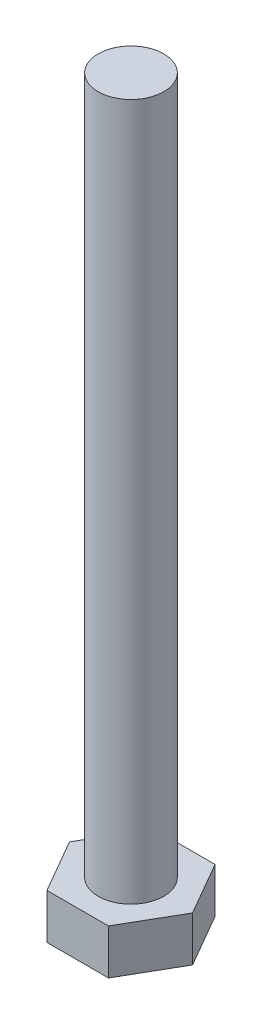
SolidWorks part; units mm, degrees
material "Plain Carbon Steel"
ref_plane "Front Plane" through (0, 0, 0) normal (0, 0, 1) x (1, 0, 0)
ref_plane "Top Plane" through (0, 0, 0) normal (0, 1, 0) x (1, 0, 0)
ref_plane "Right Plane" through (0, 0, 0) normal (1, 0, 0) x (0, 0, -1)
sketch "Sketch2" plane through (0, 0, 0) normal (0, 1, 0) x (1, 0, 0)
  line L1 (-7.5056, 0) -> (-3.7528, -6.5)
  line L2 (-3.7528, -6.5) -> (3.7528, -6.5)
  line L3 (3.7528, -6.5) -> (7.5056, 0)
  line L4 (7.5056, 0) -> (3.7528, 6.5)
  line L5 (3.7528, 6.5) -> (-3.7528, 6.5)
  line L6 (-3.7528, 6.5) -> (-7.5056, 0)
  circle A0 centre (0, 0) radius 6.5 construction
  dimension "D1" = 13
extrude "Boss-Extrude1" add sketch "Sketch2" along normal blind 5.5
sketch "Sketch3" plane through (0, 5.5, 0) normal (0, 1, 0) x (1, 0, 0)
  circle A0 centre (0, 0) radius 4
  dimension "D1" = 8
extrude "Boss-Extrude2" add sketch "Sketch3" along normal blind 85
